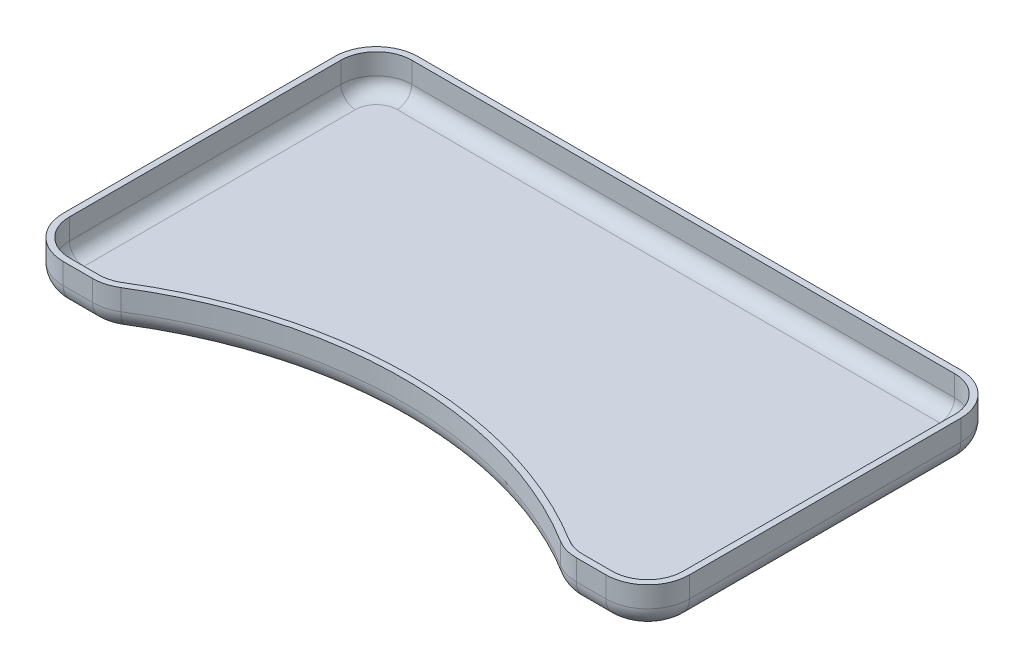
SolidWorks part; units mm, degrees
ref_plane "Front Plane" through (0, 0, 0) normal (0, 0, 1) x (1, 0, 0)
ref_plane "Top Plane" through (0, 0, 0) normal (0, 1, 0) x (1, 0, 0)
ref_plane "Right Plane" through (0, 0, 0) normal (1, 0, 0) x (0, 0, -1)
sketch "Sketch1" plane through (0, 0, 0) normal (0, 1, 0) x (1, 0, 0)
  line L0 (115.839, -85) -> (130, -85)
  line L1 (-130, 85) -> (130, 85)
  line L2 (-150, 65) -> (-150, -65)
  line L3 (-130, -85) -> (-115.839, -85)
  line L4 (150, 65) -> (150, -65)
  line L5 (-150, 85) -> (150, -85) construction
  line L6 (-150, -85) -> (150, 85) construction
  arc A0 (-105.3082, -82.003) -> (105.3082, -82.003) centre (0, -252.0329) cw
  arc A1 (-150, -65) -> (-130, -85) centre (-130, -65) ccw
  arc A2 (-105.3082, -82.003) -> (-115.839, -85) centre (-115.839, -65) cw
  arc A3 (105.3082, -82.003) -> (115.839, -85) centre (115.839, -65) ccw
  arc A4 (130, -85) -> (150, -65) centre (130, -65) ccw
  arc A5 (130, 85) -> (150, 65) centre (130, 65) cw
  arc A6 (-130, 85) -> (-150, 65) centre (-130, 65) ccw
  point P0 (0, 0)
  point P14 (-110, -85)
  point P17 (110, -85)
  dimension "D3" = 200
  dimension "D4" = 20
  dimension "D1" = 40
  dimension "D2" = 40
  dimension "D5" = 300
  dimension "D6" = 170
extrude "Boss-Extrude1" add sketch "Sketch1" along normal blind 20
fillet "Fillet1" radius 10 12 edges at (-122.9195, 0, 85) (-110.3645, 0, 84.2362) (0, 0, 52.0329) (110.3645, 0, 84.2362) (122.9195, 0, 85) (144.1421, 0, 79.1421) (150, 0, 0) (144.1421, 0, -79.1421) (0, 0, -85) (-144.1421, 0, -79.1421) (-150, 0, 0) (-144.1421, 0, 79.1421)
shell "Shell1" thickness 3
sketch "Sketch2" plane through (0, 0, 0) normal (0, -1, 0) x (1, 0, 0)
  line L1 (48.5, 20) -> (51.5, 20)
  line L2 (48.5, 20) -> (48.5, -20)
  line L3 (48.5, -20) -> (51.5, -20)
  line L4 (51.5, 20) -> (51.5, -20)
  line L5 (48.5, 20) -> (51.5, -20) construction
  line L6 (48.5, -20) -> (51.5, 20) construction
  line L7 (-51.5, 20) -> (-48.5, 20)
  line L8 (-51.5, 20) -> (-51.5, -20)
  line L9 (-51.5, -20) -> (-48.5, -20)
  line L10 (-48.5, 20) -> (-48.5, -20)
  line L11 (-51.5, 20) -> (-48.5, -20) construction
  line L12 (-51.5, -20) -> (-48.5, 20) construction
  point P0 (50, 0)
  point P5 (-50, 0)
  dimension "D1" = 50
  dimension "D2" = 3
  dimension "D3" = 40
  dimension "D4" = 50
  dimension "D5" = 3
  dimension "D6" = 40
extrude "Boss-Extrude2" add sketch "Sketch2" along normal blind 20
sketch "Sketch3" plane through (0, -20, 0) normal (0, -1, 0) x (1, 0, 0)
  line L1 (-51.5, 20) -> (51.5, 20)
  line L2 (-51.5, 20) -> (-51.5, -20)
  line L3 (-51.5, -20) -> (51.5, -20)
  line L4 (51.5, 20) -> (51.5, -20)
extrude "Boss-Extrude3" add sketch "Sketch3" along normal blind 3
sketch "Sketch4" plane through (0, -23, 0) normal (0, -1, 0) x (1, 0, 0)
  line L0 (51.5, 20) -> (-51.5, 20) construction
  circle A0 centre (0, 15) radius 1.5
  dimension "D1" = 5
extrude "Cut-Extrude1" cut sketch "Sketch4" against normal blind 3
pattern_linear "LPattern1" count 5 spacing 10 along (1, 0, 0) count 5 spacing 10 along (-1, 0, 0) of "Cut-Extrude1"
mirror "Mirror1" about plane through (0, 0, 0) normal (0, 0, 1) of "Cut-Extrude1", "LPattern1"
